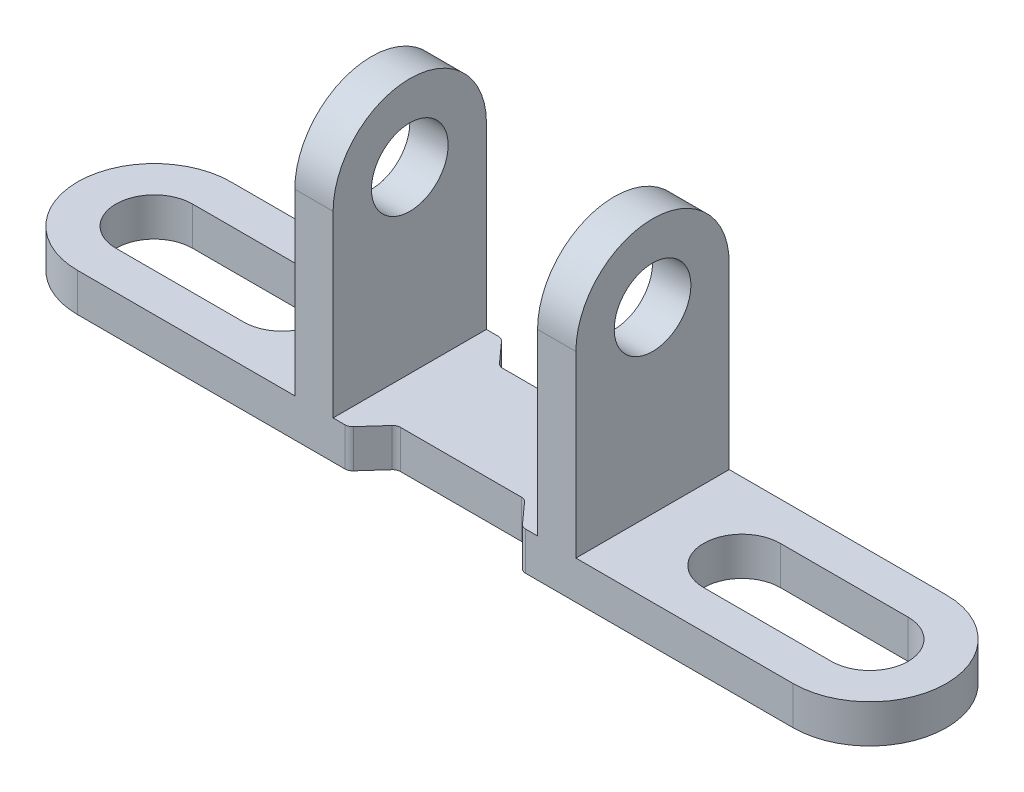
SolidWorks part; units mm, degrees
ref_plane "前视基准面" through (0, 0, 0) normal (0, 0, 1) x (1, 0, 0)
ref_plane "上视基准面" through (0, 0, 0) normal (0, 1, 0) x (1, 0, 0)
ref_plane "右视基准面" through (0, 0, 0) normal (1, 0, 0) x (0, 0, -1)
sketch "草图1" plane through (0, 0, 0) normal (0, 0, 1) x (1, 0, 0)
  line L0 (-19.4528, 0) -> (23.2864, 0) construction
  line L1 (-17, 0) -> (17, 0)
  line L2 (17, 0) -> (17, 1.5)
  line L3 (17, 1.5) -> (5.5, 1.5)
  line L4 (5.5, 1.5) -> (5.5, 11.5)
  line L5 (5.5, 11.5) -> (4, 11.5)
  line L6 (4, 11.5) -> (4, 1.5)
  line L7 (4, 1.5) -> (-4, 1.5)
  line L8 (-4, 1.5) -> (-4, 11.5)
  line L9 (-4, 11.5) -> (-5.5, 11.5)
  line L10 (-5.5, 11.5) -> (-5.5, 1.5)
  line L11 (-5.5, 1.5) -> (-17, 1.5)
  line L12 (-17, 1.5) -> (-17, 0)
  line L14 (0, 0) -> (0, 16.9372) construction
  dimension "D1" = 1.5
  dimension "D2" = 34
  dimension "D3" = 8
  dimension "D4" = 1.5
  dimension "D5" = 11.5
extrude "凸台-拉伸1" add sketch "草图1" along normal blind 6
sketch "草图2" plane through (0, 0, 0) normal (0, -1, 0) x (1, 0, 0)
  line L0 (-17, 6) -> (17, 6) construction
  line L1 (-17, 6) -> (-17, 0) construction
  line L2 (-17, 0) -> (17, 0) construction
  line L3 (17, 6) -> (17, 0) construction
  line L4 (-17, 6) -> (-14, 6)
  line L5 (-17, 6) -> (-17, 0)
  line L6 (-17, 0) -> (-14, 0)
  line L7 (17, 6) -> (17, 0)
  line L8 (14, 6) -> (17, 6)
  line L9 (14, 0) -> (17, 0)
  arc A0 (-14, 6) -> (-14, 0) centre (-14, 3) ccw
  arc A1 (14, 0) -> (14, 6) centre (14, 3) ccw
  line M1 (-17, 0) -> (17, 0)
  line M2 (17, 0) -> (17, 6)
  line M3 (17, 6) -> (-17, 6)
  line M4 (-17, 6) -> (-17, 0)
extrude "切除-拉伸1" cut sketch "草图2" against normal through all contours A0 M3 M4 | A0 L5 M1 | A1 M1 M2 | A1 L7 M3
sketch "草图3" plane through (0, 0, 0) normal (0, -1, 0) x (1, 0, 0)
  line L0 (-9, 3) -> (-14, 3) construction
  line L1 (-9, 1.5) -> (-14, 1.5)
  line L2 (-9, 4.5) -> (-14, 4.5)
  line L3 (9, 3) -> (14, 3) construction
  line L4 (9, 4.5) -> (14, 4.5)
  line L5 (9, 1.5) -> (14, 1.5)
  line L6 (0, 0) -> (0, 9.4835) construction
  arc A0 (-9, 1.5) -> (-9, 4.5) centre (-9, 3) ccw
  arc A1 (-14, 4.5) -> (-14, 1.5) centre (-14, 3) ccw
  arc A2 (9, 4.5) -> (9, 1.5) centre (9, 3) ccw
  arc A3 (14, 1.5) -> (14, 4.5) centre (14, 3) ccw
  point P2 (-11.5, 3)
  point P9 (11.5, 3)
  dimension "D1" = 3
  dimension "D2" = 5
  dimension "D3" = 5
extrude "切除-拉伸2" cut sketch "草图3" against normal through all
sketch "草图4" plane through (5.5, 0, 0) normal (1, 0, 0) x (0, 0, -1)
  line L0 (-6, 11.5) -> (0, 11.5) construction
  line L1 (-6, 1.5) -> (-6, 11.5) construction
  line L2 (0, 1.5) -> (0, 11.5) construction
  line L3 (-6, 11.5) -> (0, 11.5)
  line L4 (-6, 8.5) -> (-6, 11.5)
  line L5 (0, 1.5) -> (0, 11.5)
  arc A0 (0, 8.5) -> (-6, 8.5) centre (-3, 8.5) ccw
  circle A1 centre (-3, 8.5) radius 1.5
  line M2 (0, 11.5) -> (-6, 11.5)
  line M3 (-6, 11.5) -> (-6, 1.5)
  dimension "D1" = 3
extrude "切除-拉伸3" cut sketch "草图4" against normal through all contours A0 L3 M3 | A0 L5 M2 | A1
sketch "草图5" plane through (0, 1.5, 0) normal (0, 1, 0) x (1, 0, 0)
  line L0 (4, 0) -> (-4, 0) construction
  line L1 (4, -6) -> (-4, -6) construction
  line L2 (3.4, 0) -> (-3.4, 0)
  line L3 (4, -6) -> (-4, -6)
  line L4 (-2.5, -1) -> (2.5, -1)
  line L5 (2.5, -1) -> (3.4, 0)
  line L6 (0, 0.599) -> (0, -6.7748) construction
  line L7 (-2.5, -1) -> (-3.4, 0)
  line L8 (-4, -3) -> (4, -3) construction
  line L9 (-4, -6) -> (-4, 0) construction
  line L10 (4, 0) -> (4, -6) construction
  line L11 (-2.5, -5) -> (-3.4, -6)
  line L12 (2.5, -5) -> (3.4, -6)
  line L13 (-2.5, -5) -> (2.5, -5)
  line L14 (3.4, -6) -> (-3.4, -6)
  line M1 (4, 0) -> (-4, 0)
  dimension "D1" = 5
  dimension "D2" = 1
  dimension "D3" = 6.8
extrude "切除-拉伸4" cut sketch "草图5" against normal through all contours L7 L4 L5 M1 | L13 L11 L3 L12
fillet "圆角1" radius 0.3 8 edges at (3.4, 0.75, 6) (-3.4, 0.75, 6) (-2.5, 0.75, 5) (2.5, 0.75, 5) (-3.4, 0.75, 0) (-2.5, 0.75, 1) (2.5, 0.75, 1) (3.4, 0.75, 0)
